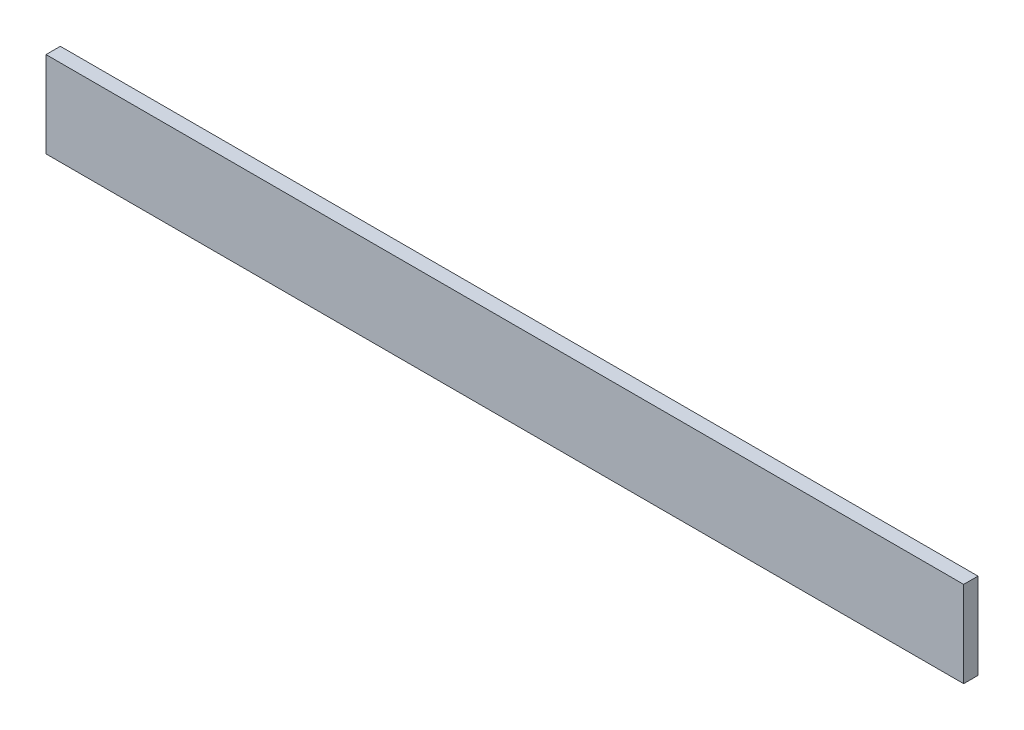
SolidWorks part; units mm, degrees
material "Acrylic (Medium-high impact)"
ref_plane "Front" through (0, 0, 0) normal (0, 0, 1) x (1, 0, 0)
ref_plane "Top" through (0, 0, 0) normal (0, 1, 0) x (1, 0, 0)
ref_plane "Right" through (0, 0, 0) normal (1, 0, 0) x (0, 0, -1)
sketch "Sketch2" plane through (0, 0, 0) normal (0, 0, 1) x (1, 0, 0)
  line L1 (-203.2, 38.1) -> (203.2, 38.1)
  line L2 (-203.2, 38.1) -> (-203.2, 0)
  line L3 (-203.2, 0) -> (203.2, 0)
  line L4 (203.2, 38.1) -> (203.2, 0)
  point P4 (0, 0)
  dimension "D1" = 406.4
  dimension "D2" = 38.1
extrude "Boss-Extrude1" add sketch "Sketch2" along normal blind 6.35
